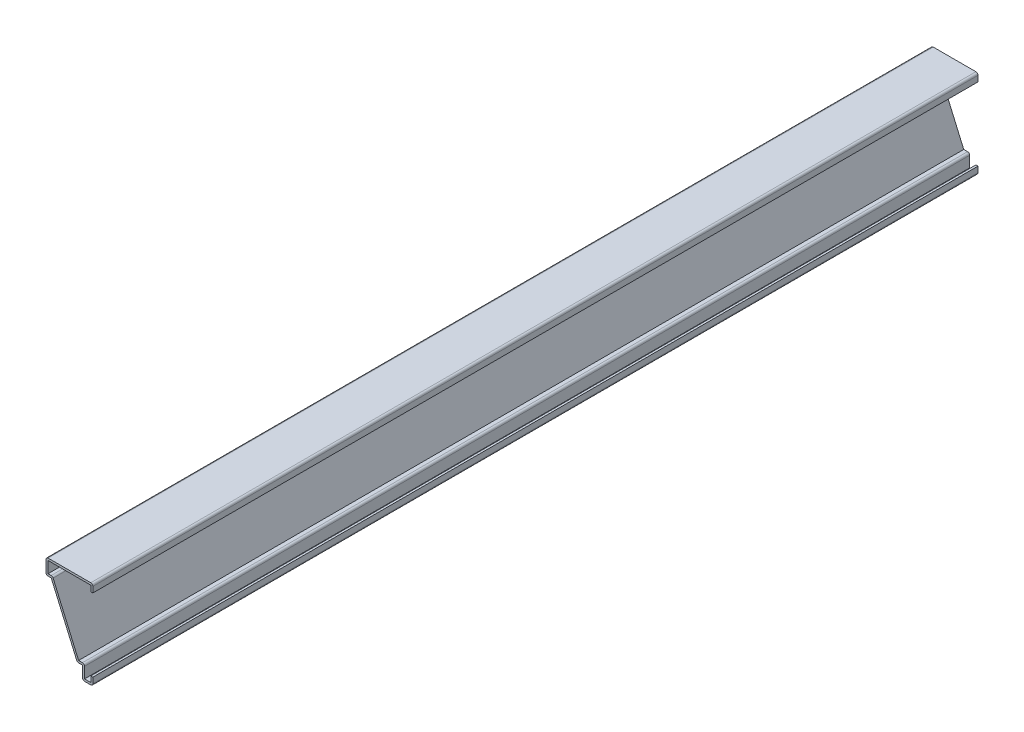
SolidWorks part; units mm, degrees
ref_plane "Front Plane" through (0, 0, 0) normal (0, 0, 1) x (1, 0, 0)
ref_plane "Top Plane" through (0, 0, 0) normal (0, 1, 0) x (1, 0, 0)
ref_plane "Right Plane" through (0, 0, 0) normal (1, 0, 0) x (0, 0, -1)
sketch "Sketch1" plane through (0, 0, 0) normal (0, 0, 1) x (1, 0, 0)
  line L0 (0, 49.2125) -> (0, 53.975)
  line L1 (0, 53.975) -> (-28.575, 53.975)
  line L2 (-28.575, 53.975) -> (-28.575, 44.45)
  line L3 (-28.575, 44.45) -> (-25.4, 44.45)
  line L4 (-25.4, 44.45) -> (-9.525, 7.9375)
  line L5 (-9.525, 7.9375) -> (-6.35, 7.9375)
  line L6 (-6.35, 7.9375) -> (-6.35, 0)
  line L7 (-6.35, 0) -> (0, 0)
  line L8 (0, 0) -> (0, 4.7625)
extrude "Extrude-Thin1" add sketch "Sketch1" against normal blind 539.75 thin thin type one direction reverse wall 1.27
fillet "Fillet1" radius 1.27 8 edges at (0, 0, -269.875) (-6.35, 0, -269.875) (-5.08, 9.2075, -269.875) (-9.525, 7.9375, -269.875) (-24.5673, 45.72, -269.875) (-28.575, 44.45, -269.875) (-28.575, 53.975, -269.875) (0, 53.975, -269.875)
equation "\"D1@Extrude-Thin1\"=\"D10@Sketch1\"*10"
